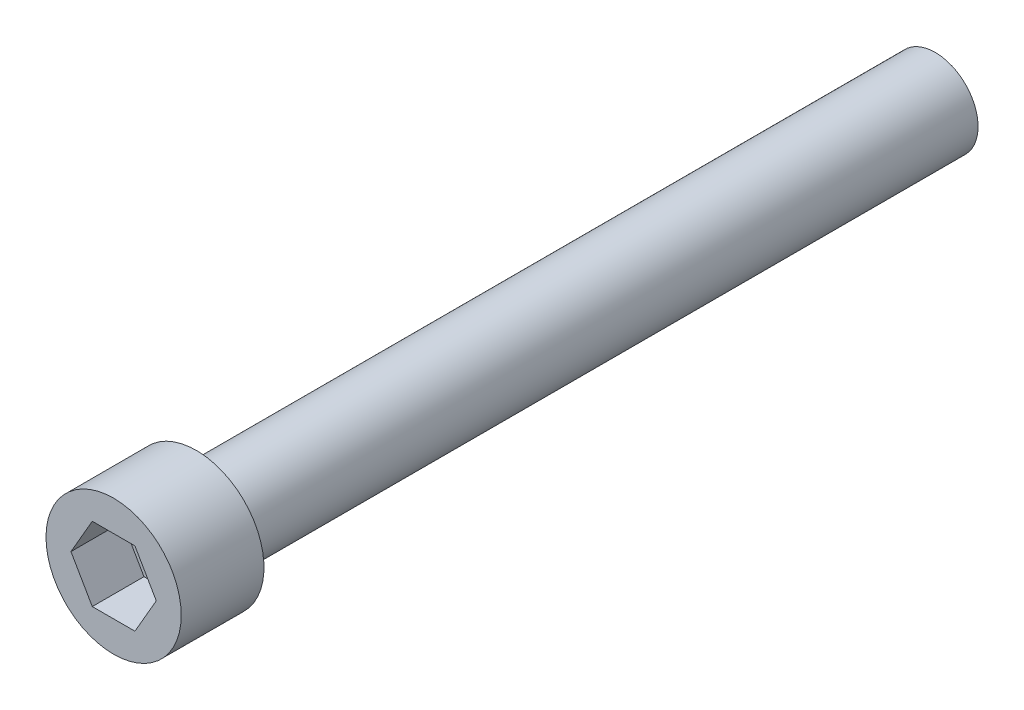
SolidWorks part; units mm, degrees
material "Alloy Steel"
ref_plane "Front Plane" through (0, 0, 0) normal (0, 0, 1) x (1, 0, 0)
ref_plane "Top Plane" through (0, 0, 0) normal (0, 1, 0) x (1, 0, 0)
ref_plane "Right Plane" through (0, 0, 0) normal (1, 0, 0) x (0, 0, -1)
sketch "Sketch1" plane through (0, 0, 0) normal (0, 0, 1) x (1, 0, 0)
  circle A0 centre (0, 0) radius 2.3241
extrude "Extrude1" add sketch "Sketch1" along normal blind 28.2448
sketch "Sketch3" plane through (0, 0, 0) normal (0, 0, -1) x (-1, 0, 0)
  circle A0 centre (0, 0) radius 1.4732
extrude "Extrude2" cut sketch "Sketch3" against normal blind 25.4 flip side to cut
sketch "Sketch4" plane through (0, 0, 28.2448) normal (0, 0, 1) x (1, 0, 0)
  line L1 (1.4665, 0) -> (0.7332, 1.27)
  line L2 (0.7332, 1.27) -> (-0.7332, 1.27)
  line L3 (-0.7332, 1.27) -> (-1.4665, 0)
  line L4 (-1.4665, 0) -> (-0.7332, -1.27)
  line L5 (-0.7332, -1.27) -> (0.7332, -1.27)
  line L6 (0.7332, -1.27) -> (1.4665, 0)
  circle A0 centre (0, 0) radius 1.27 construction
extrude "Extrude3" cut sketch "Sketch4" against normal blind 1.778
